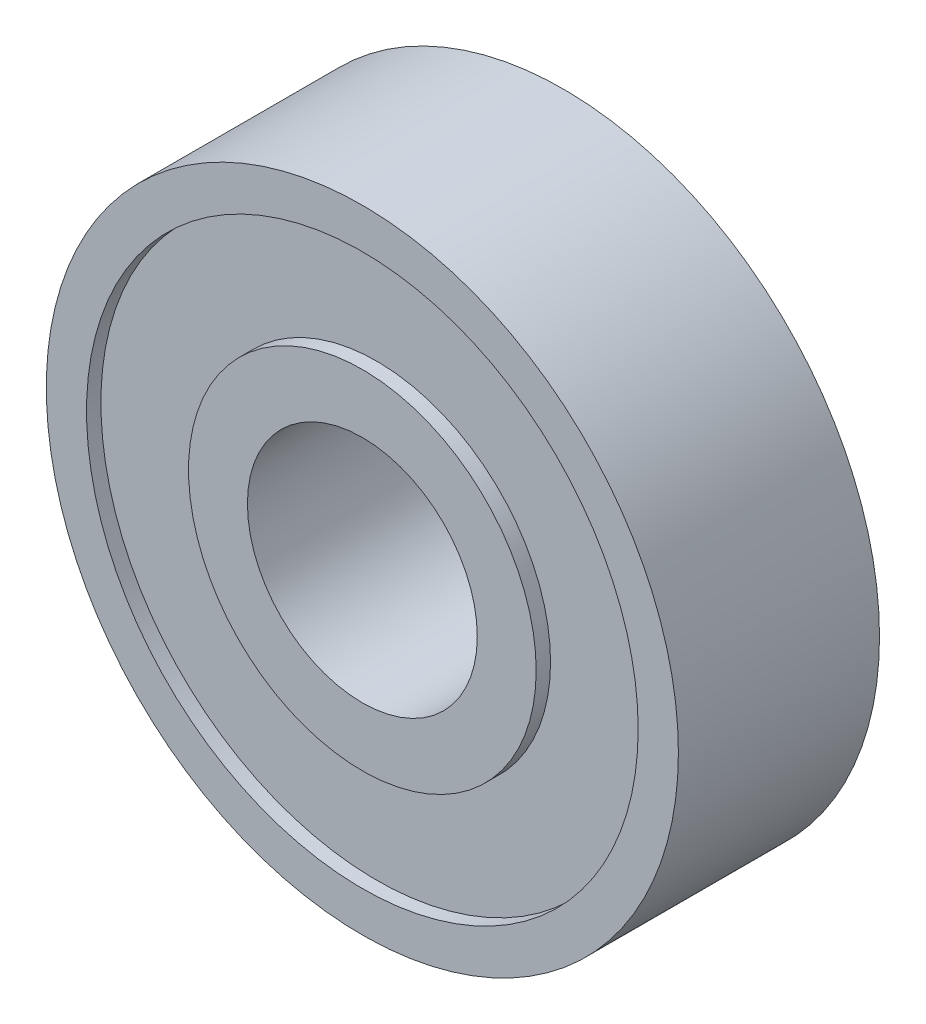
SolidWorks part; units mm, degrees
material "201 退火不鏽鋼 (SS)"
ref_plane "前基準面" through (0, 0, 0) normal (0, 0, 1) x (1, 0, 0)
ref_plane "上基準面" through (0, 0, 0) normal (0, 1, 0) x (1, 0, 0)
ref_plane "右基準面" through (0, 0, 0) normal (1, 0, 0) x (0, 0, -1)
sketch "草圖1" plane through (0, 0, 0) normal (0, 0, 1) x (1, 0, 0)
  circle A0 centre (0, 0) radius 11
  dimension "D1" = 22
extrude "填料-伸長1" add sketch "草圖1" along normal mid plane 7
sketch "草圖2" plane through (0, 0, 3.5) normal (0, 0, 1) x (1, 0, 0)
  circle A0 centre (0, 0) radius 4
  dimension "D1" = 8
extrude "除料-伸長1" cut sketch "草圖2" against normal through all
sketch "草圖3" plane through (0, 0, 3.5) normal (0, 0, 1) x (1, 0, 0)
  circle A0 centre (0, 0) radius 6.05
  circle A1 centre (0, 0) radius 9.6
  dimension "D1" = 12.1
  dimension "D2" = 19.2
extrude "除料-伸長2" cut sketch "草圖3" against normal blind 0.5
mirror "鏡射1" about plane through (0, 0, 0) normal (0, 0, 1) of "除料-伸長2"
